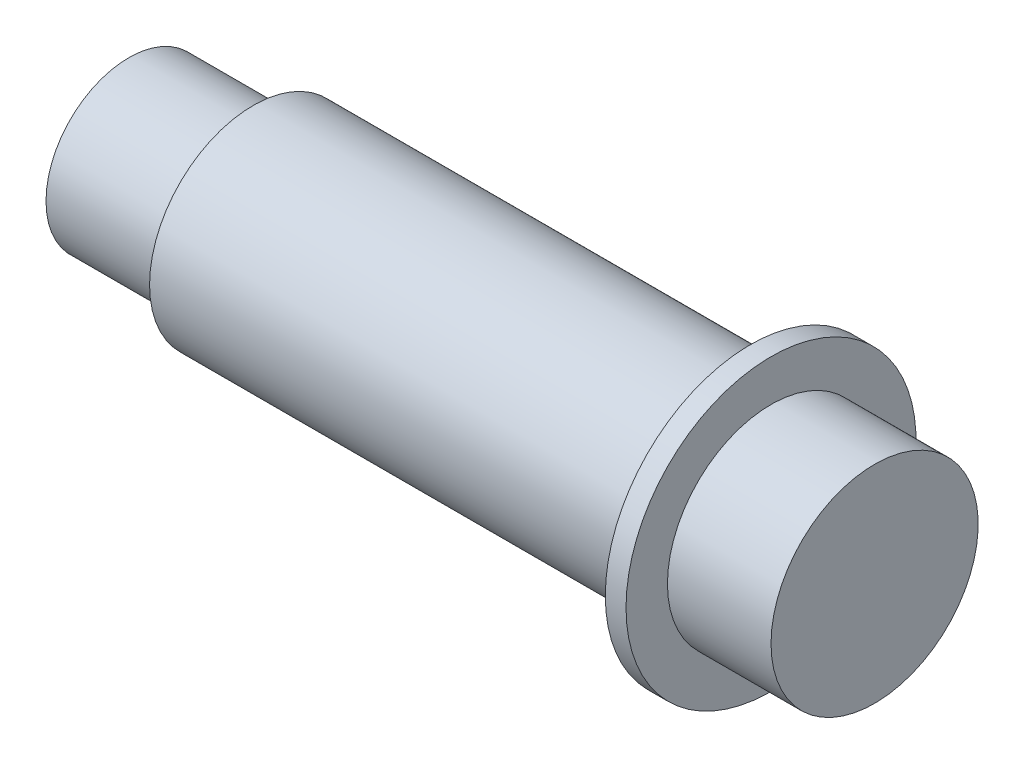
SolidWorks part; units mm, degrees
ref_plane "Ebene vorne" through (0, 0, 0) normal (0, 0, 1) x (1, 0, 0)
ref_plane "Ebene oben" through (0, 0, 0) normal (0, 1, 0) x (1, 0, 0)
ref_plane "Ebene rechts" through (0, 0, 0) normal (1, 0, 0) x (0, 0, -1)
sketch "Skizze1" plane through (0, 0, 0) normal (0, 0, 1) x (1, 0, 0)
  line L0 (0, 0) -> (21.6752, 0) construction
  line L1 (0, 0) -> (0, 2)
  line L2 (0, 2) -> (3, 2)
  line L3 (3, 2) -> (3, 2.5)
  line L4 (3, 2.5) -> (15, 2.5)
  line L5 (15, 2.5) -> (15, 3.5)
  line L6 (15, 3.5) -> (15.5, 3.5)
  line L7 (15.5, 3.5) -> (15.5, 2.5)
  line L8 (15.5, 2.5) -> (18, 2.5)
  line L9 (18, 2.5) -> (18, 0)
  line L10 (18, 0) -> (0, 0)
  dimension "D1" = 5
  dimension "D2" = 0.5
  dimension "D3" = 3
  dimension "D4" = 18
  dimension "D5" = 3
  dimension "D6" = 4
  dimension "D7" = 7
revolve "Rotation1" add sketch "Skizze1" angle 360 about L0
